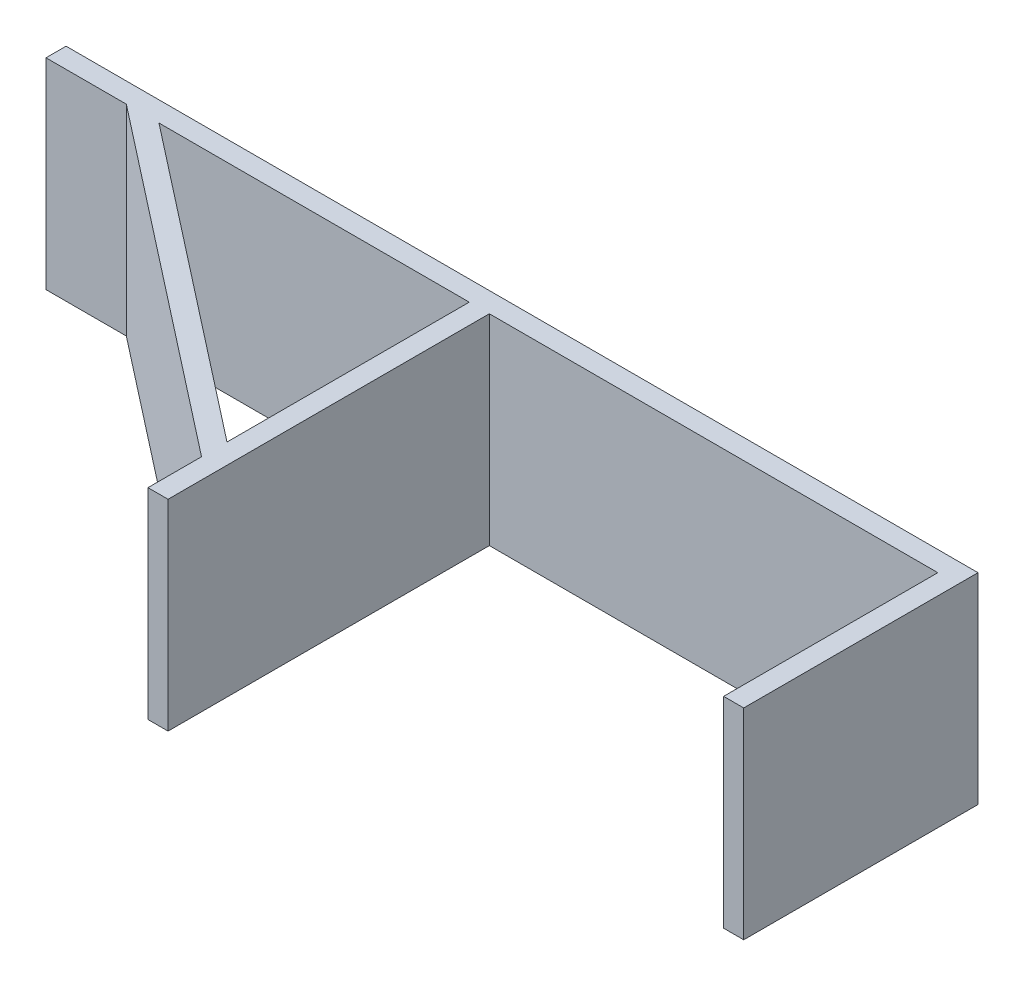
SolidWorks part; units mm, degrees
ref_plane "Front Plane" through (0, 0, 0) normal (0, 0, 1) x (1, 0, 0)
ref_plane "Top Plane" through (0, 0, 0) normal (0, 1, 0) x (1, 0, 0)
ref_plane "Right Plane" through (0, 0, 0) normal (1, 0, 0) x (0, 0, -1)
ref_plane "Plane1" through (0, 10, 0) normal (0, 1, 0) x (1, 0, 0)
sketch "Sketch1" plane through (0, 10, 0) normal (0, 1, 0) x (1, 0, 0)
  line L3 (71.5, -22) -> (71.5, 13)
  line L4 (71.5, 13) -> (-64.7348, 13)
  line L5 (-64.7348, 13) -> (-64.7348, 10)
  line L6 (-64.7348, 10) -> (-52.7348, 10)
  line L7 (-52.7348, 10) -> (-1.5, -30)
  line L8 (-1.5, -30) -> (-1.5, -38)
  line L9 (-1.5, -38) -> (1.5, -38)
  line L10 (1.5, -38) -> (1.5, 10)
  line L11 (1.5, 10) -> (68.5, 10)
  line L12 (68.5, 10) -> (68.5, -22)
  line L13 (68.5, -22) -> (71.5, -22)
  point P14 (0, 0)
  point P15 (0, 0)
  dimension "D1" = 67
  dimension "D2" = 3
  dimension "D3" = 3
  dimension "D4" = 3
  dimension "D5" = 48
  dimension "D6" = 35
  dimension "D7" = 3
  dimension "D8" = 12
  dimension "D9" = 8
  dimension "D10" = 65
extrude "Boss-Extrude2" add sketch "Sketch1" along normal blind 30
sketch "Sketch4" plane through (0, 10, 0) normal (0, -1, 0) x (1, 0, 0)
  line L0 (-47.8598, -10) -> (-1.5, 26.194)
  line L1 (-1.5, 26.194) -> (-1.5, -10)
  line L2 (-1.5, -10) -> (-47.8598, -10)
  line L3 (71.5, -13) -> (-64.7348, -13) construction
  line L4 (1.5, 38) -> (1.5, -10) construction
  line L5 (-52.7348, -10) -> (-1.5, 30) construction
  point P7 (-47.8598, -10)
  point P8 (-47.8598, -10)
  point P9 (0, 0)
  dimension "D1" = 3
  dimension "D2" = 3
  dimension "D3" = 3
extrude "Cut-Extrude1" cut sketch "Sketch4" against normal blind 30
